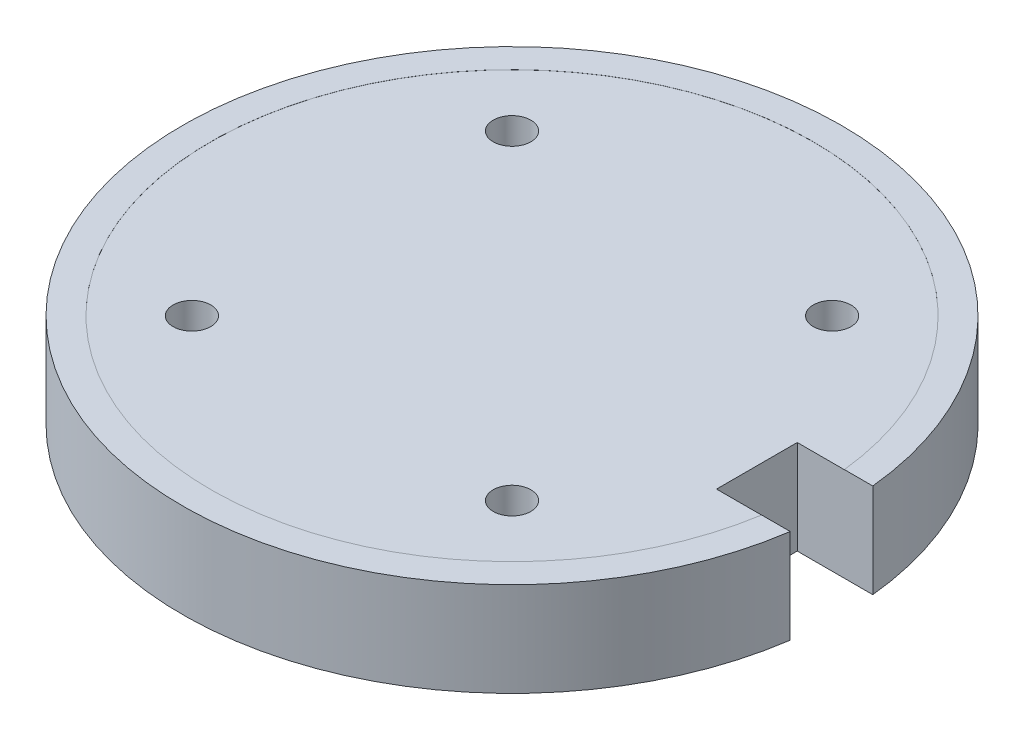
SolidWorks part; units mm, degrees
ref_plane "Front Plane" through (0, 0, 0) normal (0, 0, 1) x (1, 0, 0)
ref_plane "Top Plane" through (0, 0, 0) normal (0, 1, 0) x (1, 0, 0)
ref_plane "Right Plane" through (0, 0, 0) normal (1, 0, 0) x (0, 0, -1)
sketch "Sketch1" plane through (0, 0, 0) normal (0, 1, 0) x (1, 0, 0)
  circle A0 centre (0, 0) radius 35
  dimension "D1" = 70
extrude "Boss-Extrude1" add sketch "Sketch1" along normal blind 10
sketch "Sketch27" plane through (0, 10, 0) normal (0, 1, 0) x (1, 0, 0)
  line L1 (35.2528, 3.4921) -> (26.8023, 3.4921)
  line L2 (35.2528, 3.4921) -> (35.2528, -5.0808)
  line L3 (35.2528, -5.0808) -> (26.8023, -5.0808)
  line L4 (26.8023, 3.4921) -> (26.8023, -5.0808)
  line L5 (35.2528, 3.4921) -> (26.8023, -5.0808) construction
  line L6 (35.2528, -5.0808) -> (26.8023, 3.4921) construction
  point P0 (31.0276, -0.7944)
extrude "Cut-Extrude8" cut sketch "Sketch27" against normal through all
sketch "Sketch28" plane through (0, 10, 0) normal (0, 1, 0) x (1, 0, 0)
sketch "Sketch34" plane through (0, 10, 0) normal (0, 1, 0) x (1, 0, 0)
  circle A0 centre (-17, 17) radius 2
extrude "Cut-Extrude9" cut sketch "Sketch34" against normal through all and the other way through all
sketch "Sketch35" plane through (0, 0, 0) normal (0, -1, 0) x (-1, 0, 0)
  circle A0 centre (-17, 17) radius 2
extrude "Cut-Extrude10" cut sketch "Sketch35" against normal through all
sketch "Sketch36" plane through (0, 0, 0) normal (0, -1, 0) x (-1, 0, 0)
  circle A0 centre (17, -17) radius 2
extrude "Cut-Extrude11" cut sketch "Sketch36" against normal through all
sketch "Sketch37" plane through (0, 0, 0) normal (0, -1, 0) x (1, 0, 0)
  circle A0 centre (17, 17) radius 2
extrude "Cut-Extrude12" cut sketch "Sketch37" against normal through all
sketch "Sketch39" plane through (0, 10, 0) normal (0, 1, 0) x (1, 0, 0)
  circle A0 centre (0, 0) radius 32
extrude "Cut-Extrude14" cut sketch "Sketch39" against normal blind 0.01
